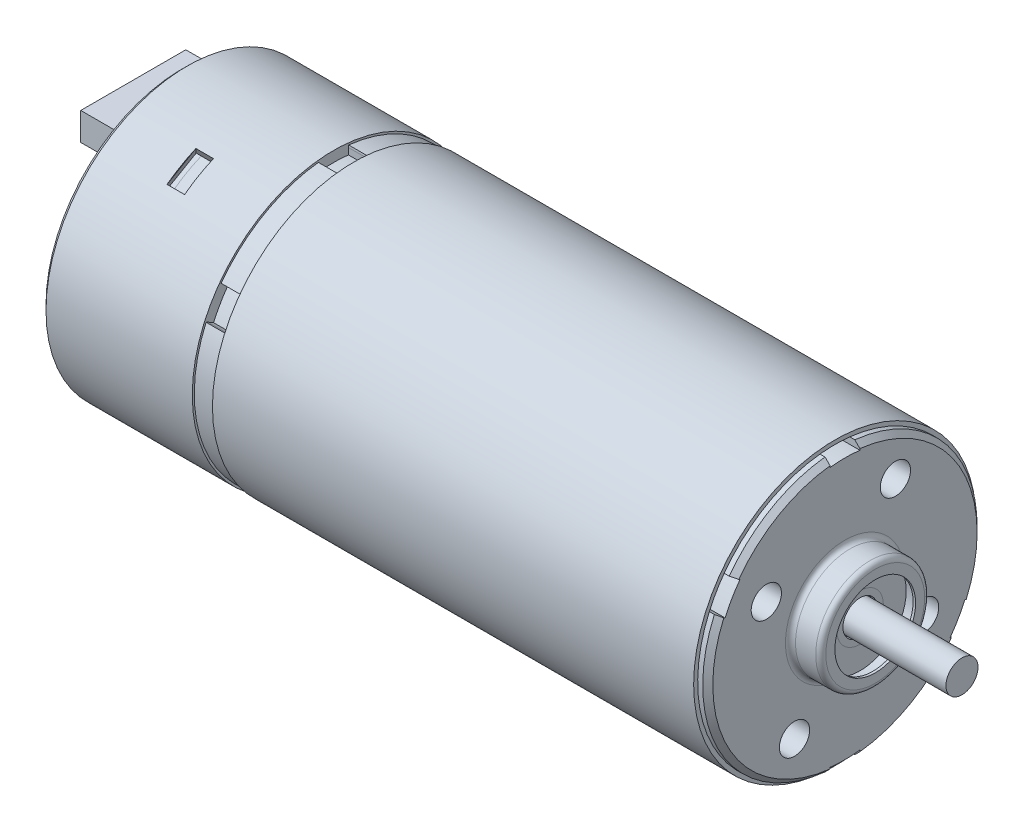
SolidWorks part; units mm, degrees
ref_plane "Front Plane" through (0, 0, 0) normal (0, 0, 1) x (1, 0, 0)
ref_plane "Top Plane" through (0, 0, 0) normal (0, 1, 0) x (1, 0, 0)
ref_plane "Right Plane" through (0, 0, 0) normal (1, 0, 0) x (0, 0, -1)
sketch "Sketch1" plane through (0, 0, 0) normal (1, 0, 0) x (0, 0, -1)
  circle A0 centre (0, 0) radius 13.6
extrude "Boss-Extrude1" add sketch "Sketch1" against normal blind 50.7
sketch "Sketch2" plane through (0, 0, 0) normal (1, 0, 0) x (0, 0, -1)
  line L0 (0, 0) -> (0, 13.6) construction
  line L1 (0, 0) -> (-13.6, 0) construction
  line L3 (-1.4767, 12.8723) -> (-1.4767, 14.3728)
  line L4 (-1.4767, 14.3728) -> (1.4767, 14.3728)
  line L5 (1.4767, 12.8723) -> (1.4767, 14.3728)
  line L6 (-1.3673, 12.8844) -> (1.4767, 14.3728) construction
  line L7 (-1.4767, 14.3728) -> (1.3673, 12.8844) construction
  line L8 (-1.4767, -14.3728) -> (1.3673, -12.8844) construction
  line L9 (-1.3673, -12.8844) -> (1.4767, -14.3728) construction
  line L10 (1.4767, -12.8723) -> (1.4767, -14.3728)
  line L11 (-1.4767, -14.3728) -> (1.4767, -14.3728)
  line L12 (-1.4767, -12.8723) -> (-1.4767, -14.3728)
  line L13 (11.8861, -5.1574) -> (13.1855, -5.9076)
  line L14 (13.1855, -5.9076) -> (11.7089, -8.4652)
  line L15 (10.4095, -7.715) -> (11.7089, -8.4652)
  line L16 (-11.8861, 5.1574) -> (-13.1855, 5.9076)
  line L17 (-11.7089, 8.4652) -> (-13.1855, 5.9076)
  line L18 (-10.4095, 7.715) -> (-11.7089, 8.4652)
  line L19 (0, 0) -> (11.7779, -6.8) construction
  line L20 (11.8419, -5.2581) -> (11.7089, -8.4652) construction
  line L21 (13.1855, -5.9076) -> (10.4746, -7.6263) construction
  line L22 (-11.7089, 8.4652) -> (-11.8419, 5.2581) construction
  line L23 (-10.4746, 7.6263) -> (-13.1855, 5.9076) construction
  circle A0 centre (0, 0) radius 13.6 construction
  arc A1 (1.4767, 12.8723) -> (-1.4767, 12.8723) centre (0, 0) ccw
  arc A2 (1.4767, -12.8723) -> (-1.4767, -12.8723) centre (0, 0) cw
  arc A3 (10.4095, -7.715) -> (11.8861, -5.1574) centre (0, 0) ccw
  arc A4 (-11.8861, 5.1574) -> (-10.4095, 7.715) centre (0, 0) cw
  point P34 (0, 0)
  dimension "D1" = 2
extrude "Cut-Extrude1" cut sketch "Sketch2" against normal through all
ref_plane "Plane1" through (-1, 0, 0) normal (1, 0, 0) x (0, 0, -1)
sketch "Sketch3" plane through (-1, 0, 0) normal (1, 0, 0) x (0, 0, -1)
  circle A0 centre (0, 0) radius 13.6
  circle A1 centre (0, 0) radius 14
extrude "Boss-Extrude2" add sketch "Sketch3" against normal blind 47.7 separate body
sketch "Sketch4" plane through (-50.7, 0, 0) normal (-1, 0, 0) x (0, 0, 1)
  circle A1 centre (0, 0) radius 14
extrude "Boss-Extrude3" add sketch "Sketch4" along normal blind 15 separate body
sketch "Sketch5" plane through (-50.7, 0, 0) normal (1, 0, 0) x (0, 0, -1)
  line L0 (1.4767, 13.5196) -> (1.4984, 13.7184)
  line L1 (-1.4767, 13.5196) -> (-1.4984, 13.7184)
  line L2 (12.4466, -5.481) -> (12.6297, -5.5616)
  line L3 (10.97, -8.0386) -> (11.1313, -8.1568)
  line L4 (1.4767, -13.5196) -> (1.4984, -13.7184)
  line L5 (-1.4767, -13.5196) -> (-1.4984, -13.7184)
  line L6 (-12.4466, 5.481) -> (-12.6297, 5.5616)
  line L7 (-10.97, 8.0386) -> (-11.1313, 8.1568)
  arc A0 (-12.4466, 5.481) -> (-1.4767, -13.5196) centre (0, 0) ccw construction
  arc A1 (1.4767, -13.5196) -> (10.97, -8.0386) centre (0, 0) ccw construction
  arc A2 (12.4466, -5.481) -> (1.4767, 13.5196) centre (0, 0) ccw construction
  arc A3 (-1.4767, 13.5196) -> (-10.97, 8.0386) centre (0, 0) ccw construction
  arc A4 (-12.4466, 5.481) -> (-1.4767, -13.5196) centre (0, 0) ccw
  arc A5 (1.4767, -13.5196) -> (10.97, -8.0386) centre (0, 0) ccw
  arc A6 (12.4466, -5.481) -> (1.4767, 13.5196) centre (0, 0) ccw
  arc A7 (-1.4767, 13.5196) -> (-10.97, 8.0386) centre (0, 0) ccw
  arc A8 (-12.6297, 5.5616) -> (-1.4984, -13.7184) centre (0, 0) ccw
  arc A9 (1.4984, -13.7184) -> (11.1313, -8.1568) centre (0, 0) ccw
  arc A10 (12.6297, -5.5616) -> (1.4984, 13.7184) centre (0, 0) ccw
  arc A11 (-1.4984, 13.7184) -> (-11.1313, 8.1568) centre (0, 0) ccw
  dimension "D1" = 0.2
extrude "Boss-Extrude4" add sketch "Sketch5" along normal up to surface (2 mm away) up to face at (-48.7, 0, -13.6)
sketch "Sketch6" plane through (0, 0, 0) normal (1, 0, 0) x (0, 0, -1)
  line L0 (-7.7942, 4.5) -> (7.7942, -4.5) construction
  line L1 (-5, -8.6603) -> (5, 8.6603) construction
  circle A0 centre (-5, -8.6603) radius 1.5
  circle A1 centre (5, 8.6603) radius 1.5
  circle A2 centre (-7.7942, 4.5) radius 1.5
  circle A3 centre (7.7942, -4.5) radius 1.5
  point P0 (0, 0)
  point P1 (0, 0)
  point P7 (0, 0)
extrude "Cut-Extrude2" cut sketch "Sketch6" against normal blind 7
sketch "Sketch7" plane through (0, 0, 0) normal (1, 0, 0) x (0, 0, -1)
  circle A0 centre (0, 0) radius 5.4
extrude "Boss-Extrude5" add sketch "Sketch7" along normal blind 3
sketch "Sketch8" plane through (3, 0, 0) normal (1, 0, 0) x (0, 0, -1)
  circle A0 centre (0, 0) radius 4
extrude "Cut-Extrude3" cut sketch "Sketch8" against normal blind 1.5
sketch "Sketch9" plane through (1.5, 0, 0) normal (1, 0, 0) x (0, 0, -1)
  circle A0 centre (0, 0) radius 1.7
extrude "Cut-Extrude4" cut sketch "Sketch9" against normal blind 0.5
sketch "Sketch10" plane through (1.5, 0, 0) normal (1, 0, 0) x (0, 0, -1)
  circle A0 centre (0, 0) radius 2.3
split line "Split Line1"
sketch "Sketch11" plane through (1, 0, 0) normal (1, 0, 0) x (0, 0, -1)
  circle A0 centre (0, 0) radius 1.5875
extrude "Boss-Extrude6" add sketch "Sketch11" along normal blind 10.6 separate body
sketch "Sketch12" plane through (1.5, 0, 0) normal (1, 0, 0) x (0, 0, -1)
  circle A0 centre (0, 0) radius 4
  circle A1 centre (0, 0) radius 4.5708
extrude "Cut-Extrude5" cut sketch "Sketch12" along normal blind 1.25
fillet "Fillet1" radius 0.5 2 edges at (3, 0, -5.4) (0, 0, -5.4)
chamfer "Chamfer1" distance 0.5 angle 45 5 edges at (-65.7, 0, 14) (0, -11.7779, -6.8) (0, 6.8, -11.7779) (0, 11.7779, 6.8) (0, -6.8, 11.7779)
ref_plane "Plane2" through (0, 12.1244, 7) normal (0, 0.866, 0.5) x (1, 0, 0)
sketch "Sketch13" plane through (0, 12.1244, 7) normal (0, 0.866, 0.5) x (1, 0, 0)
  line L0 (-50.7, -5.5616) -> (-50.7, 5.5616) construction
  line L1 (-50.7, 0) -> (-65.2, 0) construction
  line L2 (-65.2, -14) -> (-65.2, 14) construction
  line L4 (-57.08, -1.6532) -> (-58.82, -1.6532)
  line L5 (-57.08, -1.6532) -> (-57.08, 1.6532)
  line L6 (-57.08, 1.6532) -> (-58.82, 1.6532)
  line L7 (-58.82, -1.6532) -> (-58.82, 1.6532)
  line L8 (-57.08, -1.6532) -> (-58.82, 1.6532) construction
  line L9 (-57.08, 1.6532) -> (-58.82, -1.6532) construction
  point P8 (-57.95, 0)
extrude "Cut-Extrude6" cut sketch "Sketch13" against normal up to surface (1.1491 mm away)
sketch "Sketch14" plane through (-58.82, 0, 0) normal (1, 0, 0) x (0, 0, -1)
  line L0 (-5.2565, 12.4109) -> (-8.1199, 10.7578)
  line L2 (-8.3827, 11.2129) -> (-7.8571, 10.3026)
  line L3 (-4.9937, 11.9558) -> (-5.5193, 12.8661)
  line L4 (-8.1199, 10.7578) -> (-7.8571, 10.3026)
  line L5 (-4.9937, 11.9558) -> (-5.2565, 12.4109)
  arc A2 (-4.9937, 11.9558) -> (-7.8571, 10.3026) centre (0, 0) ccw
  arc A3 (-5.5193, 12.8661) -> (-8.3827, 11.2129) centre (0, 0) ccw
  arc A4 (-4.9937, 11.9558) -> (-7.8571, 10.3026) centre (0, 0) ccw
  dimension "D1" = 0
extrude "Cut-Extrude7" cut sketch "Sketch14" against normal blind 0.5
sketch "Sketch15" plane through (0, 0.8266, -1.4317) normal (0, -0.5, 0.866) x (1, 0, 0)
  line L0 (-58.82, 13.902) -> (-59.32, 12.8509)
  line L1 (-58.82, 13.902) -> (-58.82, 12.8509)
  line L2 (-57.08, 12.8509) -> (-59.32, 12.8509) construction
  line L3 (-58.82, 12.8509) -> (-59.32, 12.8509)
extrude "Cut-Extrude8" cut sketch "Sketch15" along normal up to surface (3.3064 mm away) up to face at (-58.4067, 10.7578, 8.1199)
sketch "Sketch16" plane through (0, 0.8266, -1.4317) normal (0, -0.5, 0.866) x (1, 0, 0)
  line L0 (-59.07, 13.3765) -> (-59.32, 12.8509)
  line L1 (-59.32, 12.8509) -> (-59.32, 13.3765)
  line L2 (-59.32, 13.3765) -> (-59.07, 13.3765) construction
  line L3 (-59.32, 12.8509) -> (-59.32, 13.3765) construction
  line L4 (-59.32, 13.3765) -> (-59.07, 13.3765)
extrude "Boss-Extrude7" add sketch "Sketch16" along normal up to surface (3.3064 mm away) up to face at (-58.5014, 10.6927, 8.0824)
ref_plane "Plane3" through (0, 0, 0) normal (0, 0.866, 0.5) x (1, 0, 0)
mirror "Mirror1" about plane through (0, 0, 0) normal (0, 0.866, 0.5) of "Cut-Extrude7", "Cut-Extrude8", "Boss-Extrude7", "Cut-Extrude6"
sketch "Sketch17" plane through (-65.7, 0, 0) normal (-1, 0, 0) x (0, 0, 1)
  line L0 (0, 13.5) -> (0, 8.7367) construction
  line L2 (-5.2073, 7.3617) -> (5.2073, 7.3617)
  line L3 (-5.2073, 7.3617) -> (-5.2073, 10.1117)
  line L4 (-5.2073, 10.1117) -> (5.2073, 10.1117)
  line L5 (5.2073, 7.3617) -> (5.2073, 10.1117)
  line L6 (-5.2073, 7.3617) -> (5.2073, 10.1117) construction
  line L7 (-5.2073, 10.1117) -> (5.2073, 7.3617) construction
  circle A0 centre (0, 0) radius 13.5 construction
  dimension "D1" = 2.75
extrude "Boss-Extrude8" add sketch "Sketch17" along normal blind 4.85 separate body
sketch "Sketch18" plane through (-70.55, 0, 0) normal (-1, 0, 0) x (0, 0, 1)
  line L0 (-5.2073, 10.1117) -> (-5.2073, 7.3617) construction
  line L3 (5.2073, 10.1117) -> (-5.2073, 10.1117) construction
  line L4 (5.2073, 7.3617) -> (5.2073, 10.1117) construction
  line L5 (-5.2073, 7.3617) -> (5.2073, 7.3617) construction
  line L6 (-5.2073, 10.1117) -> (-5.2073, 7.3617)
  line L7 (5.2073, 10.1117) -> (-5.2073, 10.1117)
  line L8 (5.2073, 7.3617) -> (5.2073, 10.1117)
  line L9 (-5.2073, 7.3617) -> (5.2073, 7.3617)
  line L10 (-4.8073, 9.7117) -> (-4.8073, 7.7617)
  line L11 (-4.8073, 7.7617) -> (4.8073, 7.7617)
  line L12 (4.8073, 7.7617) -> (4.8073, 9.7117)
  line L13 (4.8073, 9.7117) -> (-4.8073, 9.7117)
  dimension "D1" = 0.4
extrude "Cut-Extrude10" cut sketch "Sketch18" against normal up to surface (4.85 mm away) contours L10 L11 L12 L13 up to face at (-65.7, 0, 13.5)
sketch "Sketch19" plane through (-65.7, 0, 0) normal (-1, 0, 0) x (0, 0, 1)
  line L8 (5.6073, 6.9867) -> (5.6073, 10.4867)
  line L9 (5.6073, 10.4867) -> (-5.6073, 10.4867)
  line L10 (-5.6073, 10.4867) -> (-5.6073, 6.9867)
  line L11 (-5.6073, 6.9867) -> (5.6073, 6.9867)
  line L12 (-4.8073, 8.7367) -> (0, 8.7367) construction
  line L13 (-4.8073, 9.7117) -> (-4.8073, 7.7617) construction
  line L14 (-5.6073, 10.4867) -> (5.6073, 6.9867) construction
  dimension "D1" = 3.5
split line "Split Line2"
sketch "Sketch20" plane through (-65.7, 0, 0) normal (-1, 0, 0) x (0, 0, 1)
  line L0 (0, 7.7617) -> (0, 9.7117) construction
  line L1 (-4.8073, 7.7617) -> (4.8073, 7.7617) construction
  line L2 (4.8073, 9.7117) -> (-4.8073, 9.7117) construction
  circle A0 centre (0, 8.7367) radius 0.7
  circle A2 centre (1.8, 8.7367) radius 0.7
  circle A3 centre (3.6, 8.7367) radius 0.7
  circle A4 centre (-1.8, 8.7367) radius 0.7
  circle A5 centre (-3.6, 8.7367) radius 0.7
  dimension "D1" = 1.4
  dimension "D2" = 3
  dimension "D3" = 3
extrude "Boss-Extrude9" add sketch "Sketch20" along normal up to surface (4.85 mm away) up to face at (-70.55, 8.7367, 0)
